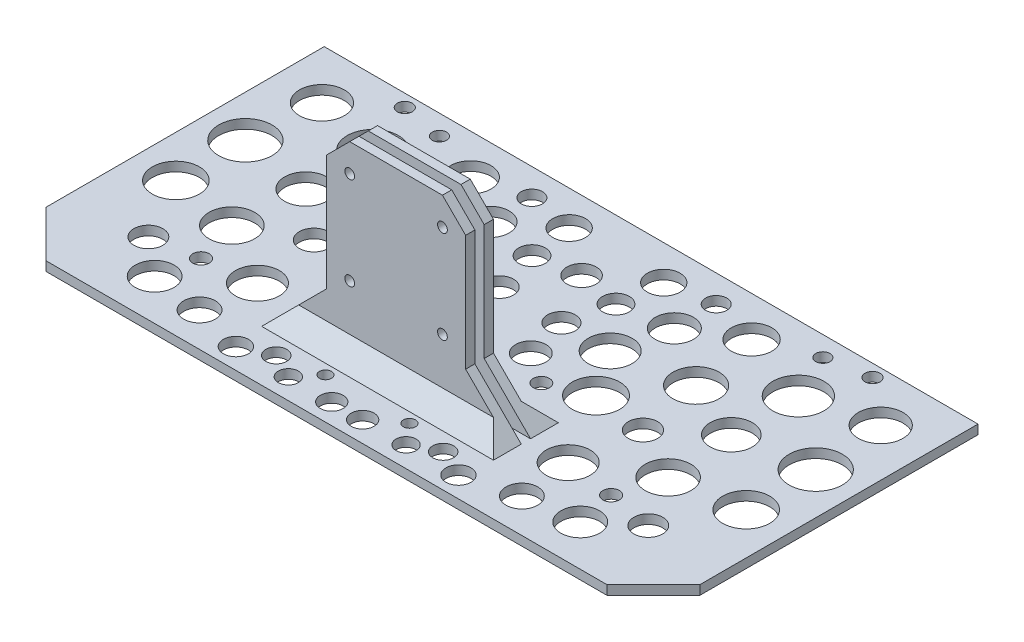
SolidWorks part; units mm, degrees
ref_plane "Front Plane" through (0, 0, 0) normal (0, 0, 1) x (1, 0, 0)
ref_plane "Top Plane" through (0, 0, 0) normal (0, 1, 0) x (1, 0, 0)
ref_plane "Right Plane" through (0, 0, 0) normal (1, 0, 0) x (0, 0, -1)
sketch "Sketch1" plane through (0, 0, 0) normal (0, 1, 0) x (1, 0, 0)
  line L1 (-70.5, -35) -> (70.5, -35)
  line L2 (-70.5, -35) -> (-70.5, 35)
  line L3 (-70.5, 35) -> (70.5, 35)
  line L4 (70.5, -35) -> (70.5, 35)
  line L5 (-70.5, -35) -> (70.5, 35) construction
  line L6 (-70.5, 35) -> (70.5, -35) construction
  point P0 (0, 0)
  dimension "D1" = 141
  dimension "D2" = 70
extrude "Boss-Extrude1" add sketch "Sketch1" along normal blind 2
sketch "Sketch2" plane through (0, 2, 0) normal (0, 1, 0) x (1, 0, 0)
  line L0 (-1000, 0) -> (49000, 0) construction
  line L1 (15, -16) -> (-15, -16)
  line L2 (15, -16) -> (15, -14)
  line L3 (15, -14) -> (-15, -14)
  line L4 (-15, -16) -> (-15, -14)
  line L5 (15, -16) -> (-15, -14) construction
  line L6 (15, -14) -> (-15, -16) construction
  line L7 (15, -20) -> (-15, -20)
  line L8 (15, -20) -> (15, -18)
  line L9 (15, -18) -> (-15, -18)
  line L10 (-15, -20) -> (-15, -18)
  line L11 (15, -20) -> (-15, -18) construction
  line L12 (15, -18) -> (-15, -20) construction
  line L13 (-70.5, -35) -> (70.5, -35) construction
  point P0 (0, -15)
  point P5 (0, -19)
  dimension "D1" = 30
  dimension "D2" = 30
  dimension "D3" = 2
  dimension "D4" = 2
  dimension "D5" = 2
  dimension "D6" = 15
extrude "Boss-Extrude2" add sketch "Sketch2" along normal blind 40
sketch "Sketch3" plane through (0, 0, 20) normal (0, 0, 1) x (1, 0, 0)
  line L0 (0, -1000) -> (0, 49000) construction
  line L1 (-70.5, 0) -> (70.5, 0) construction
  line L2 (-70.5, 2) -> (70.5, 2) construction
  circle A0 centre (-10, 16) radius 1.05
  circle A1 centre (-10, 36) radius 1.05
  circle A2 centre (10, 36) radius 1.05
  circle A3 centre (10, 16) radius 1.05
  point P17 (0, 0)
  dimension "D1" = 2.1
  dimension "D2" = 2.1
  dimension "D3" = 2.1
  dimension "D4" = 2.1
  dimension "D5" = 20
  dimension "D6" = 20
  dimension "D7" = 14
extrude "Cut-Extrude1" cut sketch "Sketch3" against normal blind 20
chamfer "Chamfer1" distance 5 angle 45 4 edges at (15, 42, 15) (15, 42, 19) (-15, 42, 15) (-15, 42, 19)
chamfer "Chamfer2" distance 10 angle 45 4 edges at (15, 2, 19) (15, 2, 15) (-15, 2, 19) (-15, 2, 15)
chamfer "Chamfer3" distance 4 angle 45 2 edges at (0, 2, 14) (0, 2, 20)
chamfer "Chamfer4" distance 10 angle 45 2 edges at (-70.5, 1, 35) (70.5, 1, 35)
sketch "Sketch4" plane through (0, 2, 0) normal (0, 1, 0) x (1, 0, 0)
  circle A0 centre (0, 20) radius 3.175
  dimension "D1" = 6.35
  dimension "D2" = 20
extrude "Cut-Extrude2" cut sketch "Sketch4" against normal blind 10
sketch "Sketch5" plane through (0, 2, 0) normal (0, 1, 0) x (1, 0, 0)
  circle A0 centre (-32.8856, 11.8117) radius 4.9746
  circle A1 centre (-35.4873, -2.2375) radius 3.1462
  circle A2 centre (-45.8941, 6.4002) radius 4.5458
  circle A3 centre (-45.8941, 20.8657) radius 5.5195
  circle A4 centre (-30.2839, 26.3852) radius 4.3745
  circle A5 centre (-19.877, 20.1372) radius 4.1235
  circle A6 centre (-17.1713, 9.0019) radius 4.7337
  circle A7 centre (-24.0006, -0.8846) radius 5.11
  circle A8 centre (-33.51, -16.3907) radius 4.7337
  circle A9 centre (-47.0389, -8.3775) radius 4.9309
  circle A10 centre (-53.9074, -19.5128) radius 3.1186
  circle A11 centre (-45.8941, -26.1732) radius 4.1861
  circle A12 centre (-34.7588, -27.6301) radius 3.4232
  circle A13 centre (-61.5043, -5.9945) radius 5.0839
  circle A14 centre (-61.5043, 9.0019) radius 5.7464
  circle A15 centre (-60.2555, 24.2607) radius 4.8291
  circle A16 centre (-50.4399, 32.3132) radius 1.6183
  circle A17 centre (-41.3483, 30.6949) radius 1.5364
  circle A18 centre (-19.877, 29.1586) radius 2.2918
  circle A19 centre (-10.1987, 27.5261) radius 3.5345
  circle A20 centre (-9.0539, 18.368) radius 2.8859
  circle A21 centre (-6.6642, 9.0019) radius 2.9837
  circle A22 centre (-9.0539, 0) radius 3.2737
  circle A23 centre (-15.7535, -4.4229) radius 1.7491
  circle A24 centre (-44.229, -17.8477) radius 1.7692
  circle A25 centre (-24.0006, -30.544) radius 2.7019
  circle A26 centre (-12.6963, -30.544) radius 2.1655
  circle A27 centre (-3.3302, -30.544) radius 2.4671
  circle A28 centre (-9.0539, -26.1732) radius 1.304
  circle A29 centre (-18.0038, -27.8421) radius 2.2503
extrude "Cut-Extrude3" cut sketch "Sketch5" against normal blind 10
mirror "Mirror1" about plane through (0, 0, 0) normal (1, 0, 0) of "Cut-Extrude3"
